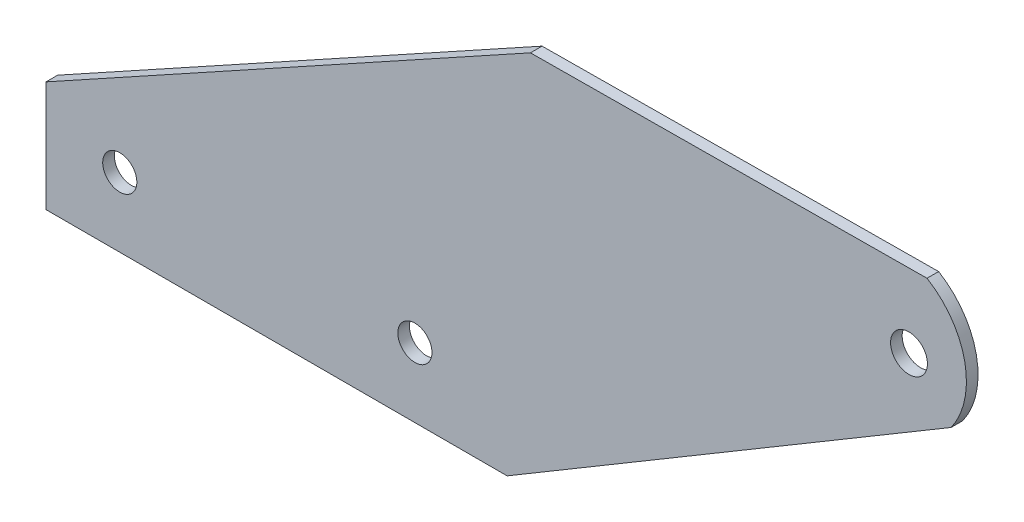
SolidWorks part; units mm, degrees
ref_plane "Front Plane" through (0, 0, 0) normal (0, 0, 1) x (1, 0, 0)
ref_plane "Top Plane" through (0, 0, 0) normal (0, 1, 0) x (1, 0, 0)
ref_plane "Right Plane" through (0, 0, 0) normal (1, 0, 0) x (0, 0, -1)
sketch "Sketch1" plane through (0, 0, 0) normal (0, 0, 1) x (1, 0, 0)
  line L0 (0, 0) -> (0, 15.24)
  line L1 (0, 15.24) -> (66.7136, 52.0603)
  line L2 (0, 0) -> (63.5, 0)
  line L3 (55, 0) -> (-55, 0) construction
  line L4 (66.7136, 52.0603) -> (121.3236, 52.4827)
  line L7 (124.6348, 36.3399) -> (63.5, 0)
  circle A2 centre (10.16, 9.525) radius 2.3495
  circle A3 centre (50.8, 9.525) radius 2.3495
  circle A5 centre (118.8416, 42.3032) radius 2.54
  arc A6 (121.3236, 52.4827) -> (124.6348, 36.3399) centre (115.5579, 42.889) cw
  dimension "D9" = 5.08
  dimension "D11" = 4.699
  dimension "D12" = 9.525
  dimension "D13" = 10.16
  dimension "D14" = 4.699
  dimension "D15" = 40.64
  dimension "D16" = 9.525
  dimension "D19" = 3.3356
  dimension "D18" = 11.193
  dimension "D2" = 63.5
  dimension "D3" = 15.24
  dimension "D4" = 76.2
  dimension "D5" = 71.12
  dimension "D6" = 54.61
  dimension "D7" = 151.548
  dimension "D8" = 28.895
  dimension "D10" = 10.16
  dimension "D17" = 30.728
extrude "Boss-Extrude1" add sketch "Sketch1" against normal blind 1.6002
